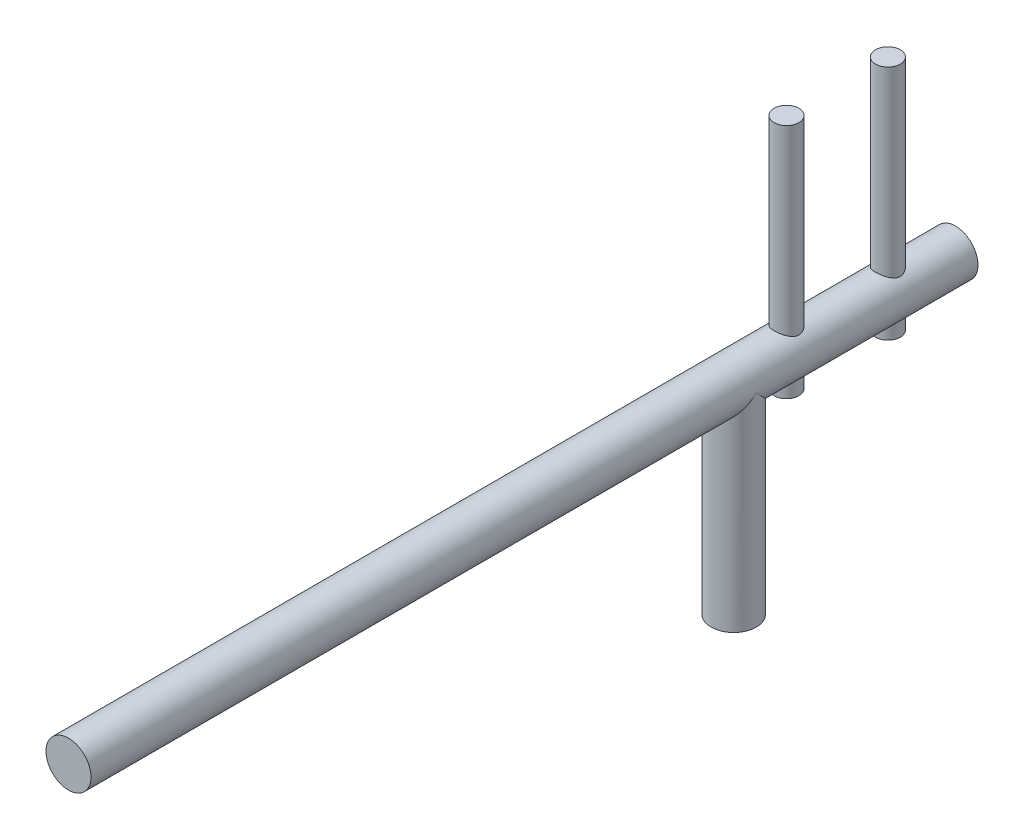
SolidWorks part; units mm, degrees
material "Maple"
ref_plane "Front Plane" through (0, 0, 0) normal (0, 0, 1) x (1, 0, 0)
ref_plane "Top Plane" through (0, 0, 0) normal (0, 1, 0) x (1, 0, 0)
ref_plane "Right Plane" through (0, 0, 0) normal (1, 0, 0) x (0, 0, -1)
sketch "Sketch1" plane through (0, 0, 0) normal (0, 1, 0) x (1, 0, 0)
  circle A0 centre (0, 0) radius 6.35
  dimension "D1" = 12.7
extrude "Boss-Extrude1" add sketch "Sketch1" along normal blind 57.15
sketch "Sketch2" plane through (0, 0, 0) normal (0, 0, 1) x (1, 0, 0)
  line L0 (6.35, 57.15) -> (-6.35, 57.15) construction
  circle A0 centre (0, 57.15) radius 6.35
extrude "Boss-Extrude2" add sketch "Sketch2" along normal blind 187.5 and the other way blind 62.5
sketch "Sketch3" plane through (0, 0, 0) normal (0, 1, 0) x (1, 0, 0)
  line L0 (0, 0) -> (0, 111.0056) construction
  line L1 (6.35, 62.5) -> (-6.35, 62.5) construction
  circle A0 centre (0, 14.875) radius 3.5
  circle A1 centre (0, 43.45) radius 3.5
  dimension "D2" = 7
  dimension "D3" = 28.575
  dimension "D4" = 7
  dimension "D1" = 19.05
extrude "Boss-Extrude3" add sketch "Sketch3" along normal blind 66.675 from offset 47.625
